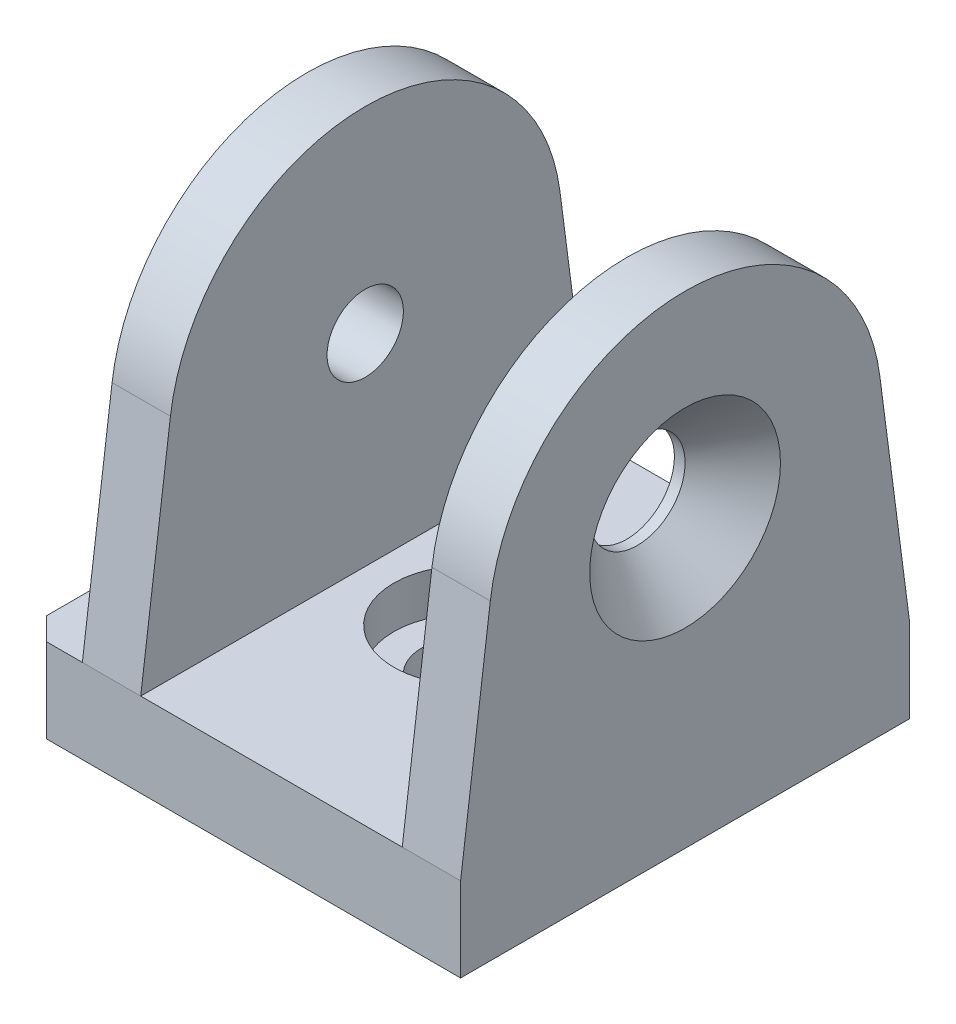
SolidWorks part; units mm, degrees
material "Алюминиевый сплав"
ref_plane "Спереди" through (0, 0, 0) normal (0, 0, 1) x (1, 0, 0)
ref_plane "Сверху" through (0, 0, 0) normal (0, 1, 0) x (1, 0, 0)
ref_plane "Справа" through (0, 0, 0) normal (1, 0, 0) x (0, 0, -1)
sketch "Эскиз1" plane through (0, 0, 0) normal (0, 1, 0) x (1, 0, 0)
  line L1 (19.45, -20) -> (-19.45, -20)
  line L2 (19.45, -20) -> (19.45, 20)
  line L3 (19.45, 20) -> (-19.45, 20)
  line L4 (-19.45, -20) -> (-19.45, 20)
  line L5 (19.45, -20) -> (-19.45, 20) construction
  line L6 (19.45, 20) -> (-19.45, -20) construction
  point P0 (0, 0)
  dimension "D1" = 38.9
  dimension "D2" = 40
extrude "Бобышка-Вытянуть1" add sketch "Эскиз1" along normal blind 7.5
sketch "Эскиз2" plane through (0, 0, 0) normal (0, 0, 1) x (1, 0, 0)
  line L1 (-19.45, 0) -> (19.45, 0) construction
  line L2 (-4, 0) -> (-4, 3.75)
  line L3 (-4, 3.75) -> (-6.5, 3.75)
  line L4 (-6.5, 3.75) -> (-6.5, 7.5)
  line L5 (-19.45, 7.5) -> (19.45, 7.5) construction
  line L7 (0, 7.5) -> (0, 0) construction
  line L11 (-19.45, 7.5) -> (-19.45, 0) construction
  line L12 (-6.5, 7.5) -> (0, 7.5)
  line L13 (0, 0) -> (-4, 0)
  line L14 (0, 0) -> (0, 7.5)
  point P17 (-19.45, 3.75)
  dimension "D1" = 8
  dimension "D2" = 13
revolve "Вырез-Повернуть1" cut sketch "Эскиз2" angle 360 about L7
sketch "Эскиз3" plane through (19.45, 0, 0) normal (1, 0, 0) x (0, 0, -1)
  line L0 (-20, 7.5) -> (-17.3526, 27.7667)
  line L1 (17.3526, 27.7667) -> (20, 7.5)
  line L2 (20, 7.5) -> (-20, 7.5)
  line L3 (-20, 0) -> (20, 0) construction
  arc A0 (-17.3526, 27.7667) -> (17.3526, 27.7667) centre (0, 25.5) cw
  dimension "D1" = 43
  dimension "D2" = 18
extrude "Бобышка-Вытянуть2" add sketch "Эскиз3" against normal blind 33.7
sketch "Эскиз4" plane through (0, 0, 0) normal (0, 0, 1) x (1, 0, 0)
  line L0 (-14.25, 7.5) -> (19.45, 7.5) construction
  line L1 (14.25, 7.5) -> (-9.05, 7.5)
  line L2 (14.25, 7.5) -> (14.25, 43)
  line L3 (14.25, 43) -> (-9.05, 43)
  line L4 (-9.05, 7.5) -> (-9.05, 43)
  line L5 (19.45, 43) -> (-14.25, 43) construction
  line L6 (14.25, 25.25) -> (19.45, 25.25) construction
  line L7 (19.45, 27.7667) -> (19.45, 7.5) construction
  line L8 (-9.05, 25.25) -> (-14.25, 25.25) construction
  line L9 (-14.25, 27.7667) -> (-14.25, 7.5) construction
  dimension "D1" = 5.2
extrude "Вырез-Вытянуть1" cut sketch "Эскиз4" against normal through all and the other way through all
chamfer "Фаска1" distance 2 angle 45 2 edges at (-19.45, 3.75, -20) (-19.45, 3.75, 20)
hole_wizard "Зенковка для винта с полупотайной головкой 1" positions "Эскиз8" profile "Эскиз10" countersink size "M8" standard "ISO" end condition up to next
sketch "Эскиз8" plane through (19.45, 0, 0) normal (1, 0, 0) x (0, 0, -1)
  point P0 (0, 25.5)
sketch "Эскиз10" plane through (19.45, 25.5, 0) normal (0, 1, 0) x (0, 0, -1)
  line L0 (0, 0) -> (0, 5.2)
  line L1 (0, 5.2) -> (4.25, 5.2)
  line L2 (4.25, 5.2) -> (4.25, 4.25)
  line L3 (4.25, 4.25) -> (8.5, 0)
  line L5 (8.5, 0) -> (0, 0)
  line L6 (-4.25, 4.25) -> (-8.5, 0) construction
  line L11 (0, -6.35) -> (0, 107.95) construction
  dimension "Диаметр сквозного отверстия" = 8.5
  dimension "Глубина сквозного отверстия" = 5.2
  dimension "Диаметр передней зенковки" = 17
  dimension "Угол передней зенковки" = 90
hole_wizard "Отверстие обработанное метчиком M81" positions "Эскиз11" profile "Эскиз13" tap size "M8" standard "ISO" end condition up to next
sketch "Эскиз11" plane through (-14.25, 0, 0) normal (-1, 0, 0) x (0, 0, 1)
  point P0 (0, 25.5)
sketch "Эскиз13" plane through (-14.25, 25.5, 0) normal (0, 1, 0) x (0, 0, 1)
  line L0 (0, 0) -> (0, 5.2)
  line L1 (0, 5.2) -> (3.4, 5.2)
  line L2 (3.4, 5.2) -> (3.4, 0)
  line L5 (3.4, 0) -> (0, 0)
  line L11 (0, -6.35) -> (0, 107.95) construction
  dimension "Диаметр проходного сверла" = 6.8
  dimension "Глубина проходного сверла" = 5.2
cosmetic thread "Отверстие резьбы2" parameters "D2"=8
